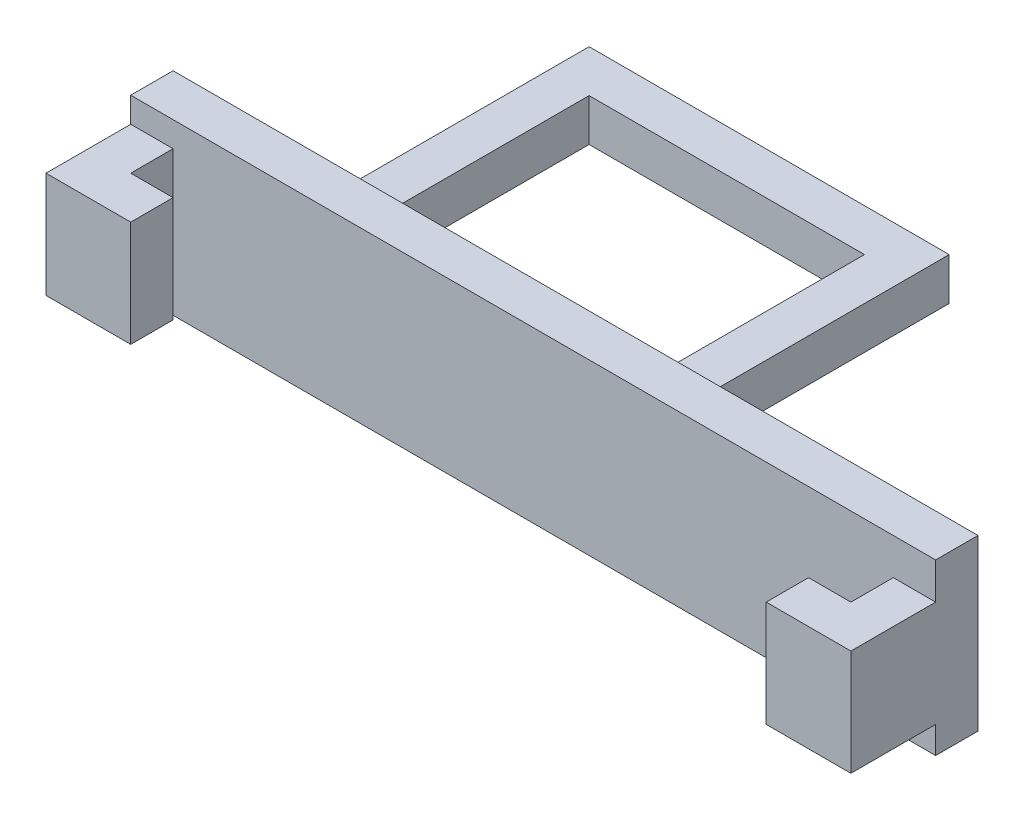
SolidWorks part; units mm, degrees
ref_plane "Front Plane" through (0, 0, 0) normal (0, 0, 1) x (1, 0, 0)
ref_plane "Top Plane" through (0, 0, 0) normal (0, 1, 0) x (1, 0, 0)
ref_plane "Right Plane" through (0, 0, 0) normal (1, 0, 0) x (0, 0, -1)
sketch "Sketch1" plane through (0, 0, 0) normal (0, 0, 1) x (1, 0, 0)
  line L1 (-1, -1) -> (1, -1)
  line L2 (-1, -1) -> (-1, 1)
  line L3 (-1, 1) -> (1, 1)
  line L4 (1, -1) -> (1, 1)
  line L5 (-1, -1) -> (1, 1) construction
  line L6 (-1, 1) -> (1, -1) construction
  point P0 (0, 0)
  dimension "D1" = 2
  dimension "D2" = 2
extrude "Boss-Extrude1" add sketch "Sketch1" along normal blind 15
sketch "Sketch4" plane through (1, 0, 0) normal (1, 0, 0) x (0, 0, -1)
  line L0 (0, 1) -> (0, -1)
  line L1 (0, 1) -> (-2, 1)
  line L2 (0, -1) -> (-2, -1)
  line L3 (-2, 1) -> (-2, -1)
  dimension "D1" = 2
extrude "Boss-Extrude3" add sketch "Sketch4" along normal blind 15
sketch "Sketch5" plane through (0, 0, 2) normal (0, 0, 1) x (1, 0, 0)
  line L0 (16, 1) -> (16, -1)
  line L1 (16, 1) -> (14, 1)
  line L2 (16, -1) -> (14, -1)
  line L3 (14, 1) -> (14, -1)
  dimension "D1" = 2
extrude "Boss-Extrude4" add sketch "Sketch5" along normal blind 11
sketch "Sketch6" plane through (0, 0, 15) normal (0, 0, 1) x (1, 0, 0)
  line L0 (-5.6399, 5.1965) -> (-5.6399, -2.8035)
  line L1 (-5.6399, 5.1965) -> (32.3601, 5.1965)
  line L2 (-5.6399, -2.8035) -> (32.3601, -2.8035)
  line L3 (32.3601, 5.1965) -> (32.3601, -2.8035)
  dimension "D1" = 38
  dimension "D2" = 8
extrude "Boss-Extrude5" add sketch "Sketch6" along normal blind 2
sketch "Sketch8" plane through (32.3601, 0, 0) normal (1, 0, 0) x (0, 0, -1)
  line L0 (-17, 3.4718) -> (-17, -1.5282)
  line L1 (-17, 3.4718) -> (-21, 3.4718)
  line L2 (-17, -1.5282) -> (-21, -1.5282)
  line L3 (-21, 3.4718) -> (-21, -1.5282)
  line L4 (-17, -2.8035) -> (-17, 5.1965) construction
  dimension "D1" = 4
  dimension "D2" = 5
extrude "Boss-Extrude6" add sketch "Sketch8" against normal blind 2
sketch "Sketch9" plane through (-5.6399, 0, 0) normal (-1, 0, 0) x (0, 0, 1)
  line L0 (17, -0.9916) -> (17, 4.0084)
  line L1 (17, -0.9916) -> (21, -0.9916)
  line L2 (17, 4.0084) -> (21, 4.0084)
  line L3 (21, -0.9916) -> (21, 4.0084)
  line L4 (17, 5.1965) -> (17, -2.8035) construction
  dimension "D1" = 5
  dimension "D2" = 4
extrude "Boss-Extrude7" add sketch "Sketch9" against normal blind 2
sketch "Sketch10" plane through (-3.6399, 0, 0) normal (1, 0, 0) x (0, 0, -1)
  line L0 (-21, 4.0084) -> (-21, -0.9916)
  line L1 (-21, 4.0084) -> (-19, 4.0084)
  line L2 (-21, -0.9916) -> (-19, -0.9916)
  line L3 (-19, 4.0084) -> (-19, -0.9916)
  dimension "D1" = 2
extrude "Boss-Extrude8" add sketch "Sketch10" along normal blind 2
sketch "Sketch11" plane through (30.3601, 0, 0) normal (-1, 0, 0) x (0, 0, 1)
  line L0 (21, 3.4718) -> (21, -1.5282)
  line L1 (21, 3.4718) -> (19, 3.4718)
  line L2 (21, -1.5282) -> (19, -1.5282)
  line L3 (19, 3.4718) -> (19, -1.5282)
  dimension "D1" = 2
extrude "Boss-Extrude9" add sketch "Sketch11" along normal blind 2
